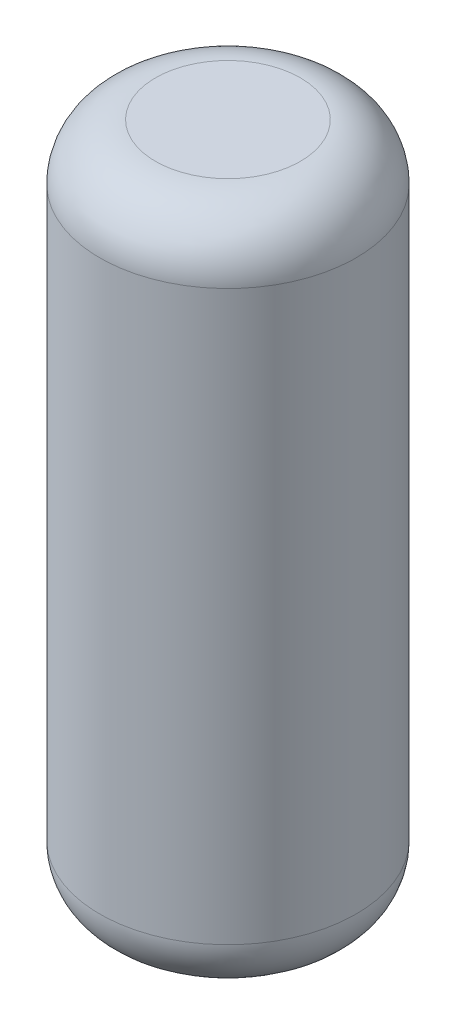
SolidWorks part; units mm, degrees
material "Thornel Mat VMA"
ref_plane "Front Plane" through (0, 0, 0) normal (0, 0, 1) x (1, 0, 0)
ref_plane "Top Plane" through (0, 0, 0) normal (0, 1, 0) x (1, 0, 0)
ref_plane "Right Plane" through (0, 0, 0) normal (1, 0, 0) x (0, 0, -1)
sketch "Sketch2" plane through (0, 0, 0) normal (0, 0, 1) x (1, 0, 0)
  line L0 (0, 232.41) -> (0, -232.41) construction
  line L1 (0, 232.41) -> (0, 156.21) construction
  line L2 (87.63, 156.21) -> (-87.63, 156.21) construction
  line L3 (0, -232.41) -> (0, -156.21) construction
  line L4 (-87.63, -156.21) -> (87.63, -156.21) construction
  line L5 (0, -232.41) -> (49.53, -232.41)
  line L6 (87.63, -194.31) -> (87.63, -156.21)
  line L7 (0, 232.41) -> (49.53, 232.41)
  line L8 (87.63, 194.31) -> (87.63, 156.21)
  line L9 (87.63, 156.21) -> (87.63, -156.21)
  line L10 (0, -232.41) -> (0, 232.41)
  arc A0 (49.53, -232.41) -> (87.63, -194.31) centre (49.53, -194.31) ccw
  arc A1 (49.53, 232.41) -> (87.63, 194.31) centre (49.53, 194.31) cw
  point P4 (0, 0)
  point P8 (0, 156.21)
  point P12 (0, -156.21)
  dimension "D6" = 38.1
  dimension "D1" = 464.82
  dimension "D2" = 76.2
  dimension "D3" = 175.26
  dimension "D4" = 76.2
  dimension "D5" = 175.26
revolve "Revolve1" add sketch "Sketch2" angle 360 about L10
sketch "Sketch3" plane through (0, -232.41, 0) normal (0, -1, 0) x (-1, 0, 0)
  circle A0 centre (0, 0) radius 12.7
  dimension "D1" = 25.4
extrude "Boss-Extrude1" add sketch "Sketch3" along normal blind 19.05
shell "Shell1" thickness 2.54
sketch "Sketch5" plane through (0, -251.46, 0) normal (0, -1, 0) x (1, 0, 0)
  circle A0 centre (0, 0) radius 7.9375
  dimension "D1" = 15.875
sketch "Sketch6" plane through (0, -251.46, 0) normal (0, -1, 0) x (-1, 0, 0)
  circle A0 centre (0, 0) radius 12.7
  dimension "D1" = 25.4
extrude "Boss-Extrude2" add sketch "Sketch6" against normal blind 25.4 from offset 6.35
sketch "Sketch7" plane through (0, -257.81, 0) normal (0, -1, 0) x (1, 0, 0)
  circle A0 centre (0, 0) radius 7.9375
  dimension "D1" = 15.875
extrude "Cut-Extrude3" cut sketch "Sketch7" against normal blind 25.4
